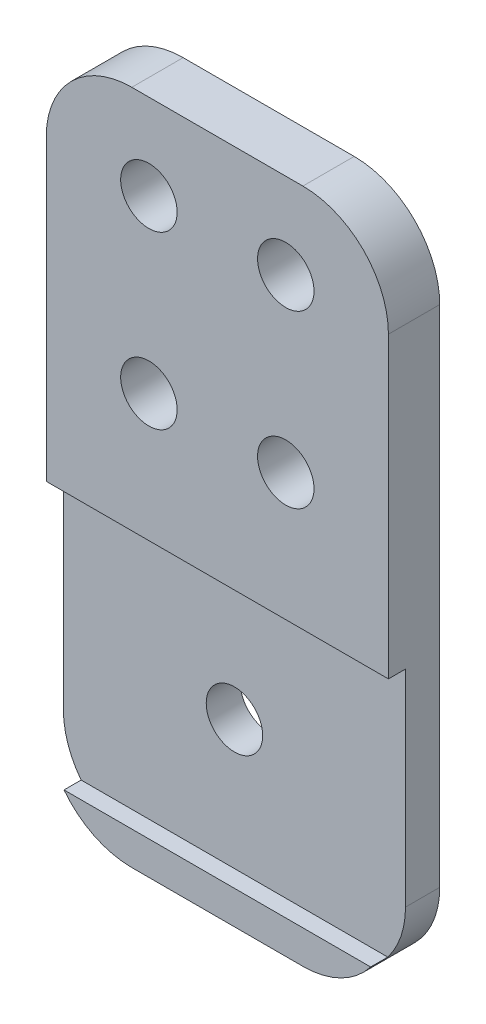
SolidWorks part; units mm, degrees
material "3.1325 (EN-AW 2017A)"
ref_plane "正面" through (0, 0, 0) normal (0, 0, 1) x (1, 0, 0)
ref_plane "平面" through (0, 0, 0) normal (0, 1, 0) x (1, 0, 0)
ref_plane "右側面" through (0, 0, 0) normal (1, 0, 0) x (0, 0, -1)
sketch "ｽｹｯﾁ2" plane through (0, 0, 0) normal (0, 0, 1) x (1, 0, 0)
  line L0 (0, 0) -> (0, -20) construction
  line L1 (-4, -5) -> (4, -5) construction
  line L2 (-4, -5) -> (-4, 5) construction
  line L3 (-4, 5) -> (4, 5) construction
  line L4 (4, -5) -> (4, 5) construction
  line L5 (-4, -5) -> (4, 5) construction
  line L6 (-4, 5) -> (4, -5) construction
  line L7 (10, -20) -> (-10, -20) construction
  line L8 (-10, -29.5) -> (10, -29.5)
  line L9 (-10, -29.5) -> (-10, 10)
  line L10 (-10, 10) -> (10, 10)
  line L11 (10, -29.5) -> (10, 10)
  line L12 (-10, -29.5) -> (10, 10) construction
  line L13 (-10, 10) -> (10, -29.5) construction
  line L15 (-10, 10) -> (10, 10)
  circle A0 centre (-4, 5) radius 1.65
  circle A1 centre (-4, -5) radius 1.65
  circle A2 centre (4, -5) radius 1.65
  circle A3 centre (4, 5) radius 1.65
  circle A4 centre (0, -20) radius 1.65
  point P0 (0, 0)
  point P13 (0, -9.75)
  point P18 (0, 0)
  point P21 (0, -20)
  point P22 (0, 0)
  point P23 (0, 0)
  dimension "D1" = 3.3
  dimension "D4" = 3.3
  dimension "D5" = 15
  dimension "D2" = 10
  dimension "D3" = 8
  dimension "D6" = 20
  dimension "D7" = 9.5
  dimension "D8" = 5
  dimension "D13" = 10
extrude "ﾎﾞｽ - 押し出し1" add sketch "ｽｹｯﾁ2" along normal blind 3
sketch "ｽｹｯﾁ3" plane through (0, 0, 3) normal (0, 0, 1) x (1, 0, 0)
  line L0 (10, -29.5) -> (10, 10) construction
  line L1 (-10, -27.55) -> (10, -27.55)
  line L2 (-10, -27.55) -> (-10, -12.45)
  line L3 (-10, -12.45) -> (10, -12.45)
  line L4 (10, -27.55) -> (10, -12.45)
  line L5 (-10, -27.55) -> (10, -12.45) construction
  line L6 (-10, -12.45) -> (10, -27.55) construction
  point P0 (0, -20)
  dimension "D1" = 15.1
extrude "ｶｯﾄ - 押し出し1" cut sketch "ｽｹｯﾁ3" against normal blind 1
fillet "ﾌｨﾚｯﾄ2" radius 5 4 edges at (-10, -29.5, 1.5) (10, -29.5, 1.5) (-10, 10, 1.5) (10, 10, 1.5)
